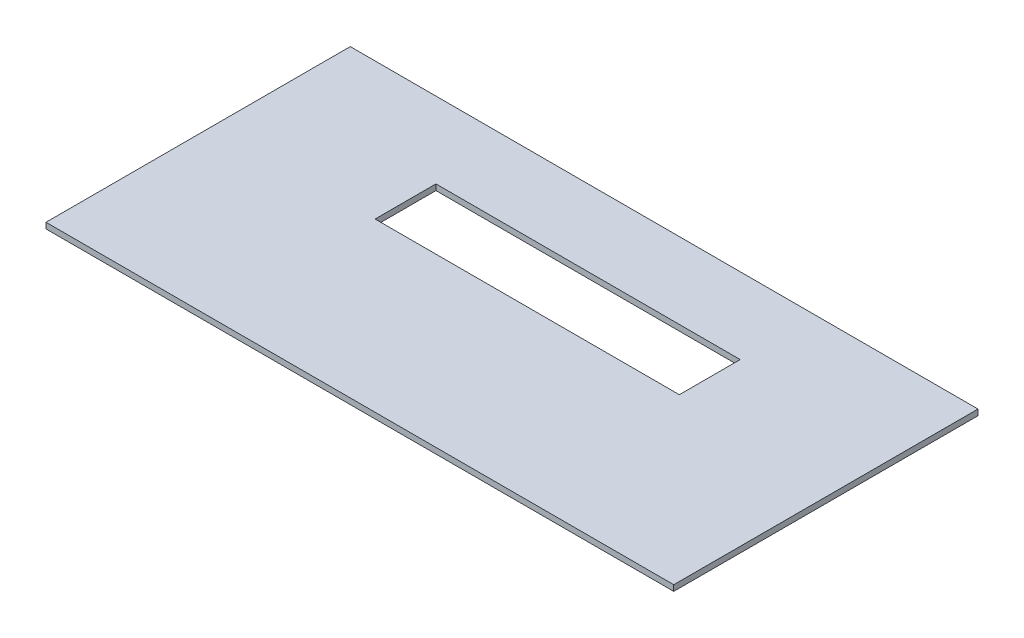
SolidWorks part; units mm, degrees
ref_plane "Front Plane" through (0, 0, 0) normal (0, 0, 1) x (1, 0, 0)
ref_plane "Top Plane" through (0, 0, 0) normal (0, 1, 0) x (1, 0, 0)
ref_plane "Right Plane" through (0, 0, 0) normal (1, 0, 0) x (0, 0, -1)
sketch "Sketch1" plane through (0, 0, 0) normal (0, 1, 0) x (1, 0, 0)
  line L1 (-65.5079, -31.75) -> (65.5079, -31.75)
  line L2 (-65.5079, -31.75) -> (-65.5079, 31.75)
  line L3 (-65.5079, 31.75) -> (65.5079, 31.75)
  line L4 (65.5079, -31.75) -> (65.5079, 31.75)
  line L5 (-65.5079, -31.75) -> (65.5079, 31.75) construction
  line L6 (-65.5079, 31.75) -> (65.5079, -31.75) construction
  point P0 (0, 0)
  dimension "D1" = 131.0157
  dimension "D2" = 63.5
extrude "Boss-Extrude1" add sketch "Sketch1" along normal blind 1.2141
sketch "Sketch2" plane through (0, 1.2141, 0) normal (0, 1, 0) x (1, 0, 0)
  line L0 (65.5079, 31.75) -> (-65.5079, 31.75) construction
  line L1 (-31.75, 3.175) -> (31.75, 3.175)
  line L2 (-31.75, 3.175) -> (-31.75, 15.875)
  line L3 (-31.75, 15.875) -> (31.75, 15.875)
  line L4 (31.75, 3.175) -> (31.75, 15.875)
  line L5 (-31.75, 3.175) -> (31.75, 15.875) construction
  line L6 (-31.75, 15.875) -> (31.75, 3.175) construction
  point P0 (0, 9.525)
  point P5 (0, 0)
  dimension "D1" = 63.5
  dimension "D2" = 12.7
  dimension "D3" = 15.875
extrude "Cut-Extrude1" cut sketch "Sketch2" against normal through all
